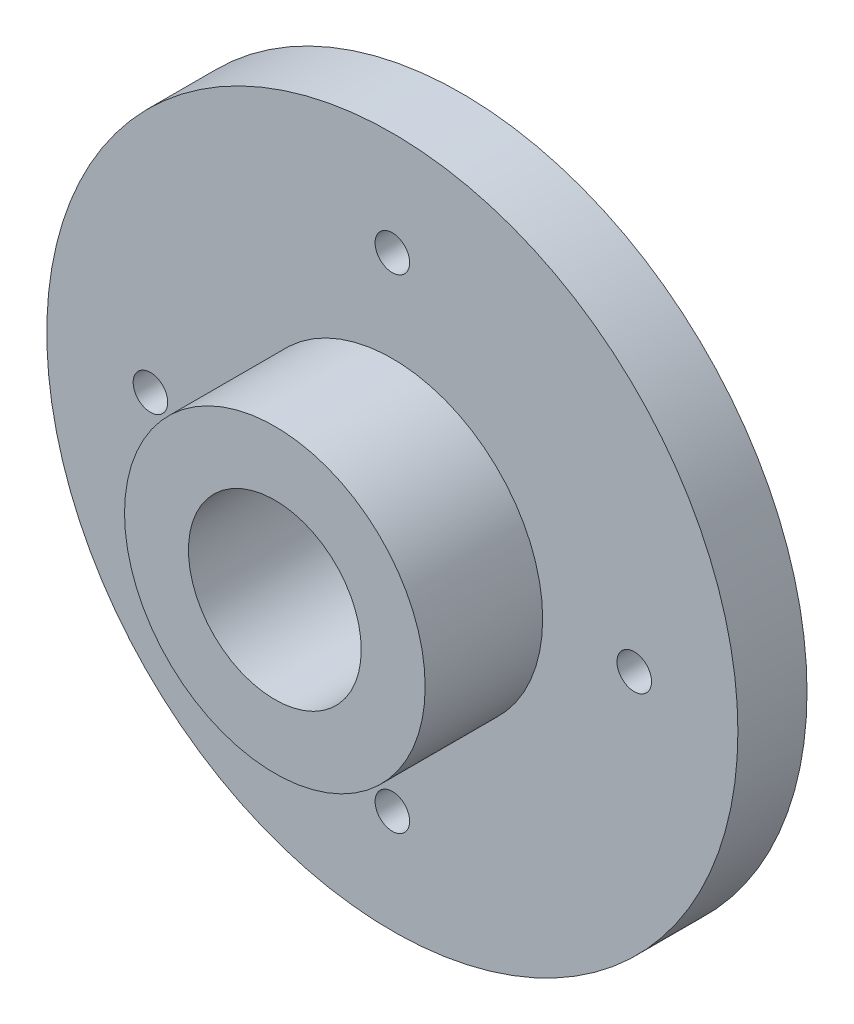
SolidWorks part; units mm, degrees
ref_plane "前视基准面" through (0, 0, 0) normal (0, 0, 1) x (1, 0, 0)
ref_plane "上视基准面" through (0, 0, 0) normal (0, 1, 0) x (1, 0, 0)
ref_plane "右视基准面" through (0, 0, 0) normal (1, 0, 0) x (0, 0, -1)
sketch "草图1" plane through (0, 0, 0) normal (0, 0, 1) x (1, 0, 0)
  circle A0 centre (0, 0) radius 10
  dimension "D1" = 20
extrude "凸台-拉伸1" add sketch "草图1" along normal blind 2
sketch "草图2" plane through (0, 0, 2) normal (0, 0, 1) x (1, 0, 0)
  circle A0 centre (0, 0) radius 4.35
  dimension "D1" = 8.7
extrude "凸台-拉伸2" add sketch "草图2" along normal blind 3.4
sketch "草图3" plane through (0, 0, 0) normal (0, 0, 1) x (1, 0, 0)
  circle A0 centre (0, 0) radius 1.5
  dimension "D1" = 3
extrude "切除-拉伸1" cut sketch "草图3" along normal blind 9.4
sketch "草图4" plane through (0, 0, 0) normal (0, 0, 1) x (1, 0, 0)
  circle A0 centre (0, 0) radius 7 construction
  circle A1 centre (0, 7) radius 0.5
  circle A2 centre (7, 0) radius 0.5
  circle A3 centre (0, -7) radius 0.5
  circle A4 centre (-7, 0) radius 0.5
  dimension "D1" = 14
  dimension "D2" = 1
  dimension "D3" = 1
  dimension "D4" = 1
  dimension "D5" = 1
extrude "切除-拉伸3" cut sketch "草图4" along normal blind 16.4
sketch "草图5" plane through (0, 0, 5.4) normal (0, 0, 1) x (1, 0, 0)
  circle A0 centre (0, 0) radius 2.5
  circle A1 centre (0, 0) radius 4.35 construction
  dimension "D1" = 1.85
extrude "切除-拉伸4" cut sketch "草图5" against normal blind 4.4
